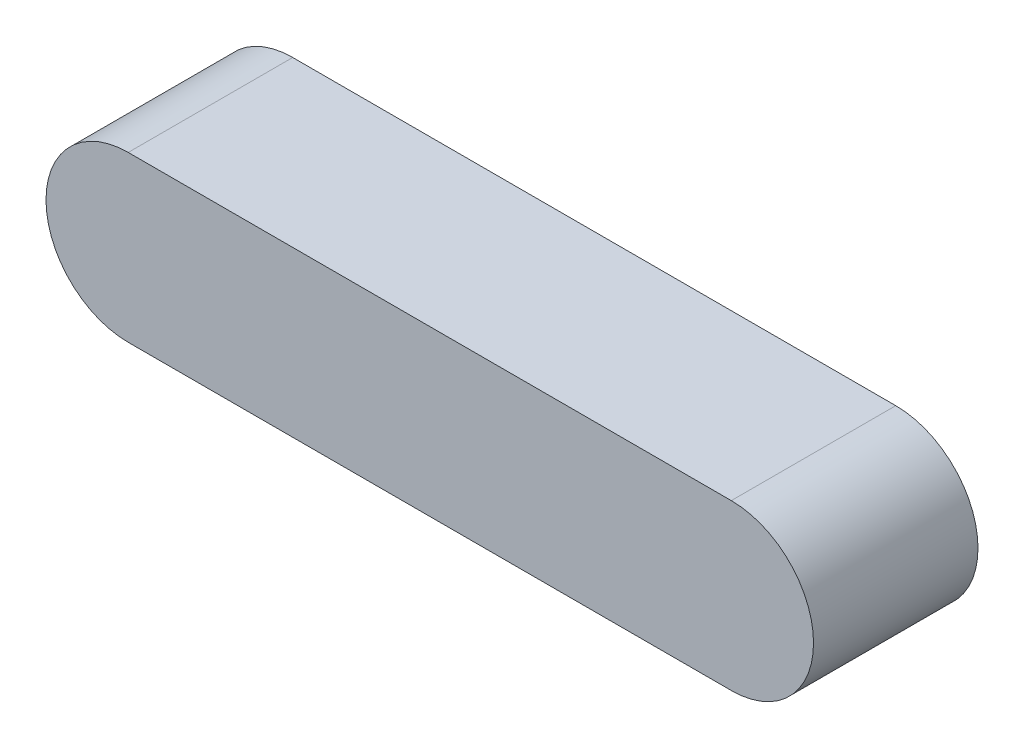
SolidWorks part; units mm, degrees
ref_plane "Front Plane" through (0, 0, 0) normal (0, 0, 1) x (1, 0, 0)
ref_plane "Top Plane" through (0, 0, 0) normal (0, 1, 0) x (1, 0, 0)
ref_plane "Right Plane" through (0, 0, 0) normal (1, 0, 0) x (0, 0, -1)
sketch "Sketch1" plane through (0, 0, 0) normal (0, 0, 1) x (1, 0, 0)
  line L0 (0, 0) -> (11, 0) construction
  line L1 (0, 1.5) -> (11, 1.5)
  line L2 (0, -1.5) -> (11, -1.5)
  arc A0 (0, 1.5) -> (0, -1.5) centre (0, 0) ccw
  arc A1 (11, -1.5) -> (11, 1.5) centre (11, 0) ccw
  point P3 (5.5, 0)
  point P8 (-1.5, 0)
  point P9 (12.5, 0)
  dimension "D1" = 1.5
  dimension "D2" = 14
extrude "Boss-Extrude1" add sketch "Sketch1" along normal blind 3
